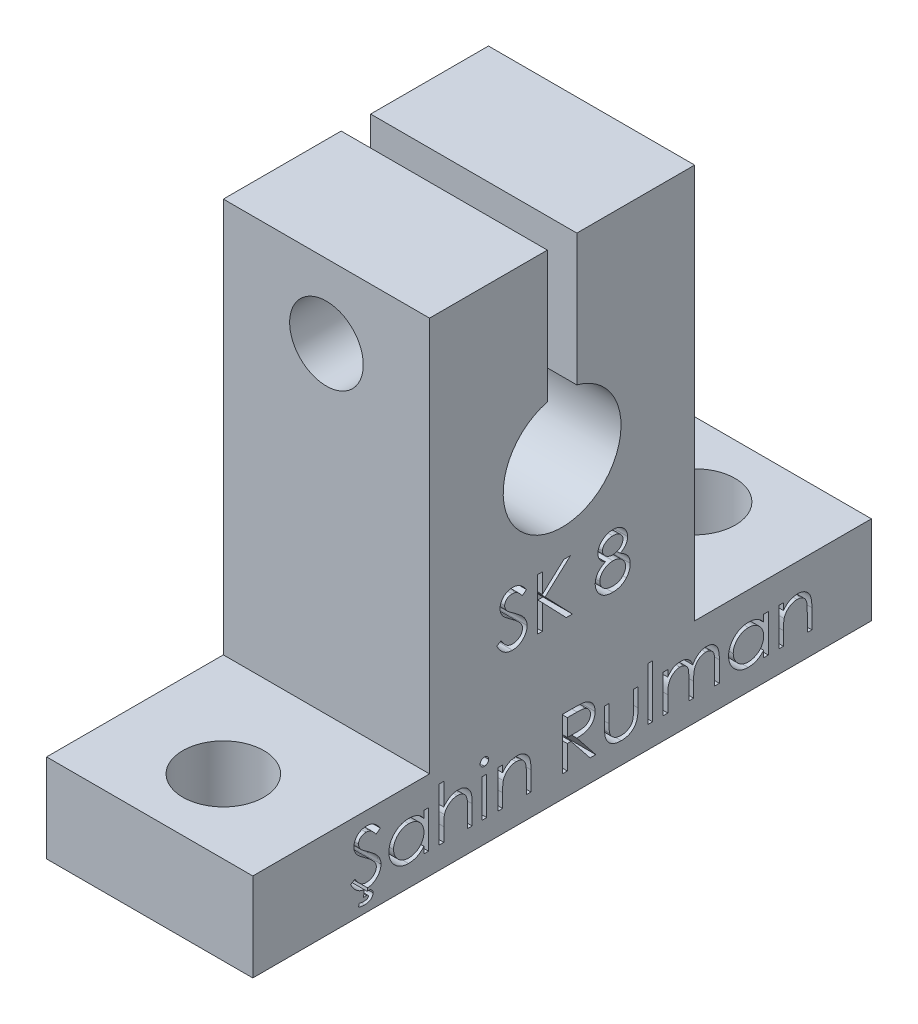
SolidWorks part; units mm, degrees
ref_plane "Front Plane" through (0, 0, 0) normal (0, 0, 1) x (1, 0, 0)
ref_plane "Top Plane" through (0, 0, 0) normal (0, 1, 0) x (1, 0, 0)
ref_plane "Right Plane" through (0, 0, 0) normal (1, 0, 0) x (0, 0, -1)
sketch "Sketch1" plane through (0, 0, 0) normal (1, 0, 0) x (0, 0, -1)
  line L0 (-21, 0) -> (21, 0)
  line L1 (-21, 0) -> (-21, 6)
  line L2 (-21, 6) -> (-9, 6)
  line L3 (-9, 6) -> (-9, 32.8)
  line L4 (-9, 32.8) -> (-1, 32.8)
  line L5 (9, 32.8) -> (9, 6)
  line L6 (9, 6) -> (21, 6)
  line L7 (21, 6) -> (21, 0)
  line L9 (1, 32.8) -> (9, 32.8)
  line L10 (1, 23.873) -> (1, 32.8)
  line L11 (-1, 23.873) -> (-1, 32.8)
  arc A0 (-1, 23.873) -> (1, 23.873) centre (0, 20) ccw
  dimension "D3" = 8
  dimension "D1" = 32.8
  dimension "D2" = 18
  dimension "D4" = 6
  dimension "D5" = 6
  dimension "D6" = 42
extrude "Boss-Extrude1" add sketch "Sketch1" along normal mid plane 14
sketch "Sketch4" plane through (0, 6, 0) normal (0, 1, 0) x (1, 0, 0)
  circle A0 centre (0, -16) radius 2.75
  circle A1 centre (0, 16) radius 2.75
  dimension "D3" = 5.5
extrude "Cut-Extrude3" cut sketch "Sketch4" against normal through all
sketch "Sketch5" plane through (7, 0, 0) normal (1, 0, 0) x (0, 0, -1)
  text T0 "Şahin Rulman"
extrude "Cut-Extrude4" cut sketch "Sketch5" against normal blind 2
sketch "Sketch6" plane through (0, 0, -9) normal (0, 0, -1) x (-1, 0, 0)
  line L0 (-7, 32.8) -> (7, 32.8) construction
  circle A0 centre (0, 27.8) radius 2.5
  dimension "D2" = 5
  dimension "D1" = 5
extrude "Cut-Extrude6" cut sketch "Sketch6" against normal through all
sketch "Sketch7" plane through (0, 0, -9) normal (0, 0, -1) x (-1, 0, 0)
  circle A0 centre (0, 27.8) radius 4
  dimension "D1" = 8
extrude "Cut-Extrude7" cut sketch "Sketch7" against normal blind 5
sketch "Sketch8" plane through (7, 0, 0) normal (1, 0, 0) x (0, 0, -1)
  text T0 "SK 8"
extrude "Cut-Extrude8" cut sketch "Sketch8" against normal blind 2
